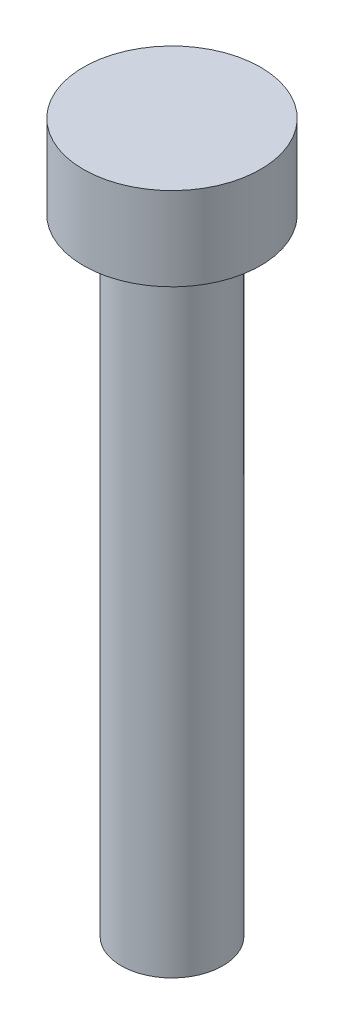
SolidWorks part; units mm, degrees
ref_plane "Front Plane" through (0, 0, 0) normal (0, 0, 1) x (1, 0, 0)
ref_plane "Top Plane" through (0, 0, 0) normal (0, 1, 0) x (1, 0, 0)
ref_plane "Right Plane" through (0, 0, 0) normal (1, 0, 0) x (0, 0, -1)
sketch "Sketch1" plane through (0, 0, 0) normal (0, 1, 0) x (1, 0, 0)
  circle A0 centre (0, 0) radius 4.25
  dimension "D1" = 8.5
extrude "Boss-Extrude1" add sketch "Sketch1" along normal blind 4
sketch "Sketch2" plane through (0, 0, 0) normal (0, -1, 0) x (1, 0, 0)
  circle A0 centre (0, 0) radius 2.44
  dimension "D1" = 4.88
extrude "Boss-Extrude2" add sketch "Sketch2" along normal blind 30
